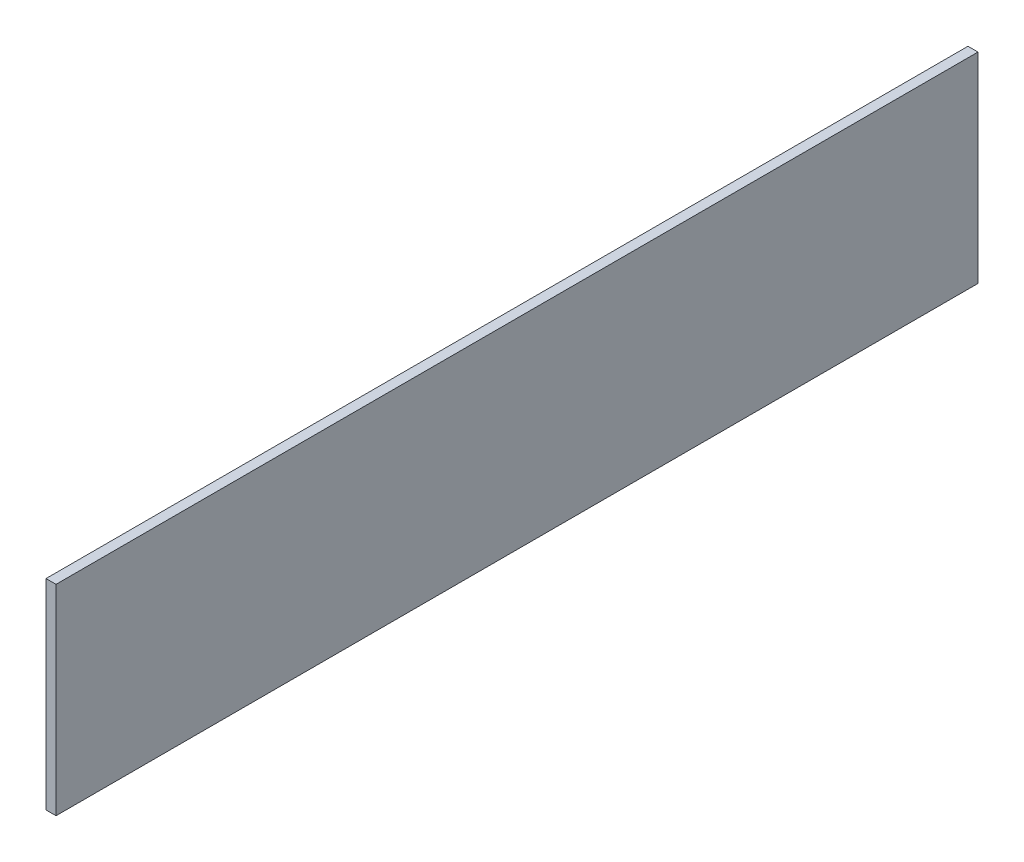
SolidWorks part; units mm, degrees
ref_plane "Plano frontal" through (0, 0, 0) normal (0, 0, 1) x (1, 0, 0)
ref_plane "Plano superior" through (0, 0, 0) normal (0, 1, 0) x (1, 0, 0)
ref_plane "Plano direito" through (0, 0, 0) normal (1, 0, 0) x (0, 0, -1)
sketch "Esboço1" plane through (0, 0, 0) normal (1, 0, 0) x (0, 0, -1)
  line L1 (0, 0) -> (2300, 0)
  line L2 (0, 0) -> (0, 500)
  line L3 (0, 500) -> (2300, 500)
  line L4 (2300, 0) -> (2300, 500)
  dimension "D1" = 2300
  dimension "D2" = 500
extrude "Ressalto-extrusão1" add sketch "Esboço1" along normal blind 25
